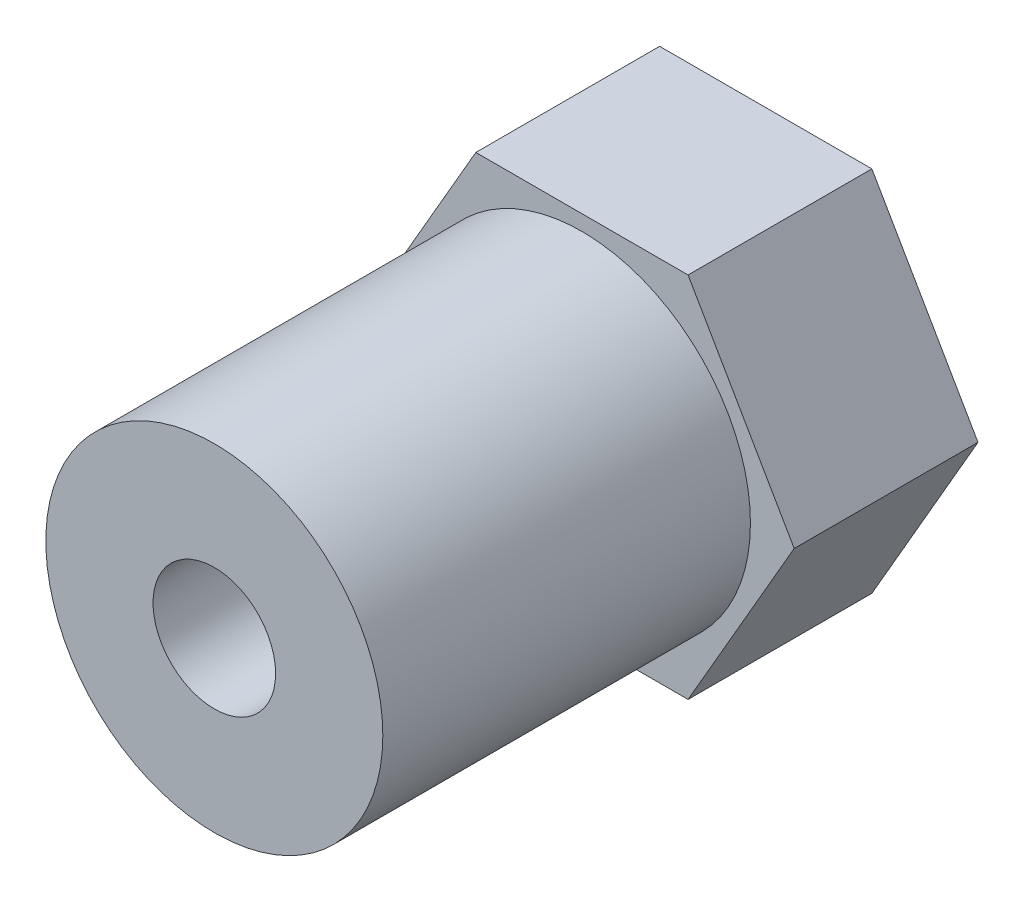
SolidWorks part; units mm, degrees
ref_plane "Front Plane" through (0, 0, 0) normal (0, 0, 1) x (1, 0, 0)
ref_plane "Top Plane" through (0, 0, 0) normal (0, 1, 0) x (1, 0, 0)
ref_plane "Right Plane" through (0, 0, 0) normal (1, 0, 0) x (0, 0, -1)
sketch "Sketch2" plane through (0, 0, 0) normal (0, 0, 1) x (1, 0, 0)
  line L1 (3.4641, -6) -> (6.9282, 0)
  line L2 (6.9282, 0) -> (3.4641, 6)
  line L3 (3.4641, 6) -> (-3.4641, 6)
  line L4 (-3.4641, 6) -> (-6.9282, 0)
  line L5 (-6.9282, 0) -> (-3.4641, -6)
  line L6 (-3.4641, -6) -> (3.4641, -6)
  circle A0 centre (0, 0) radius 6 construction
  circle A1 centre (0, 0) radius 2
  point P1 (0, 6)
  dimension "D1" = 12
extrude "Boss-Extrude1" add sketch "Sketch2" along normal blind 6
sketch "Sketch3" plane through (0, 0, 6) normal (0, 0, 1) x (1, 0, 0)
  circle A0 centre (0, 0) radius 5.5
  circle A1 centre (0, 0) radius 2
  dimension "D1" = 11
  dimension "D2" = 4
extrude "Boss-Extrude2" add sketch "Sketch3" along normal blind 12
